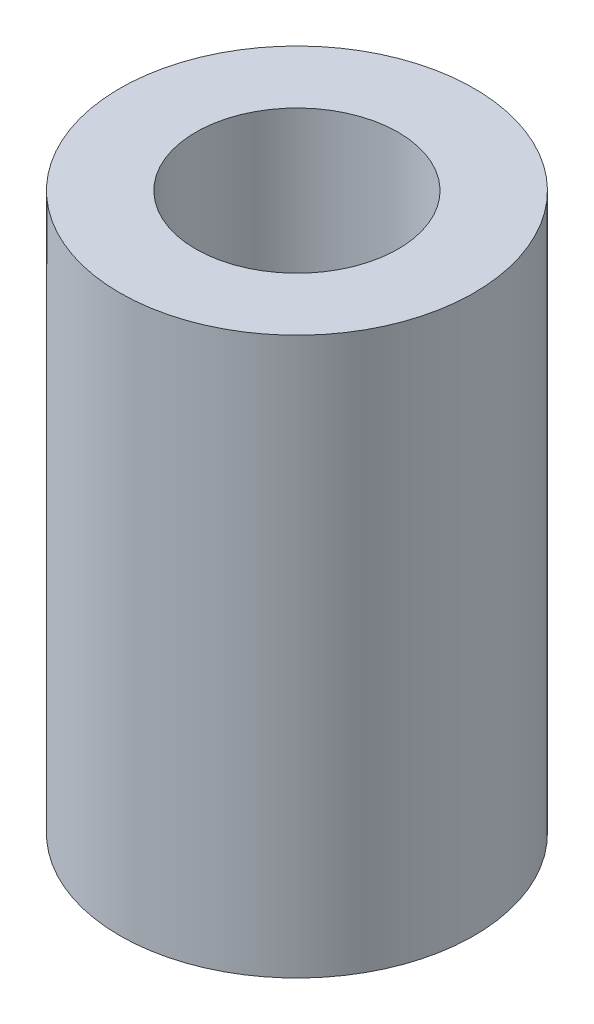
SolidWorks part; units mm, degrees
ref_plane "Front Plane" through (0, 0, 0) normal (0, 0, 1) x (1, 0, 0)
ref_plane "Top Plane" through (0, 0, 0) normal (0, 1, 0) x (1, 0, 0)
ref_plane "Right Plane" through (0, 0, 0) normal (1, 0, 0) x (0, 0, -1)
sketch "Sketch1" plane through (0, 0, 0) normal (0, 1, 0) x (1, 0, 0)
  circle A0 centre (0, 0) radius 7
  circle A1 centre (0, 0) radius 2.5
  dimension "D1" = 5
  dimension "D2" = 14
extrude "Boss-Extrude1" add sketch "Sketch1" along normal blind 22
sketch "Sketch2" plane through (0, 22, 0) normal (0, 1, 0) x (1, 0, 0)
  circle A0 centre (0, 0) radius 4
  dimension "D1" = 8
extrude "Cut-Extrude1" cut sketch "Sketch2" against normal blind 11
